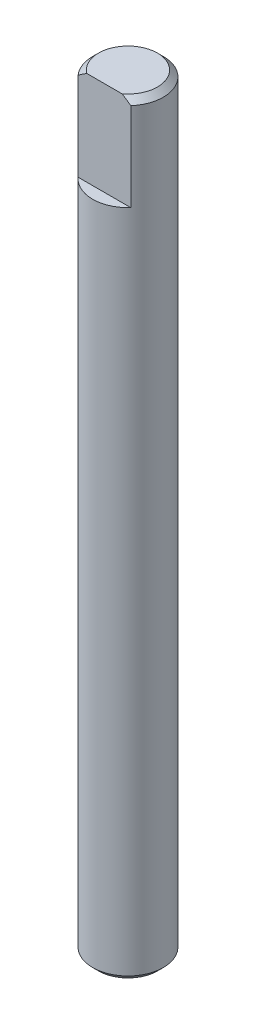
SolidWorks part; units mm, degrees
ref_plane "Front Plane" through (0, 0, 0) normal (0, 0, 1) x (1, 0, 0)
ref_plane "Top Plane" through (0, 0, 0) normal (0, 1, 0) x (1, 0, 0)
ref_plane "Right Plane" through (0, 0, 0) normal (1, 0, 0) x (0, 0, -1)
sketch "Sketch1" plane through (0, 0, 0) normal (0, 1, 0) x (1, 0, 0)
  circle A0 centre (0, 0) radius 3
  dimension "D1" = 6
extrude "Boss-Extrude1" add sketch "Sketch1" along normal blind 65
sketch "Sketch2" plane through (0, 65, 0) normal (0, 1, 0) x (1, 0, 0)
  line L0 (-2.2361, -2) -> (2.2361, -2)
  circle A0 centre (0, 0) radius 3 construction
  circle A2 centre (0, 0) radius 3
  arc A3 (-2.2361, -2) -> (2.2361, -2) centre (0, 0) ccw
  dimension "D1" = 2
  dimension "D2" = 0
extrude "Cut-Extrude1" cut sketch "Sketch2" against normal blind 8
chamfer "Chamfer1" distance 0.5 angle 45 2 edges at (0, 0, 3) (0, 65, -3)
